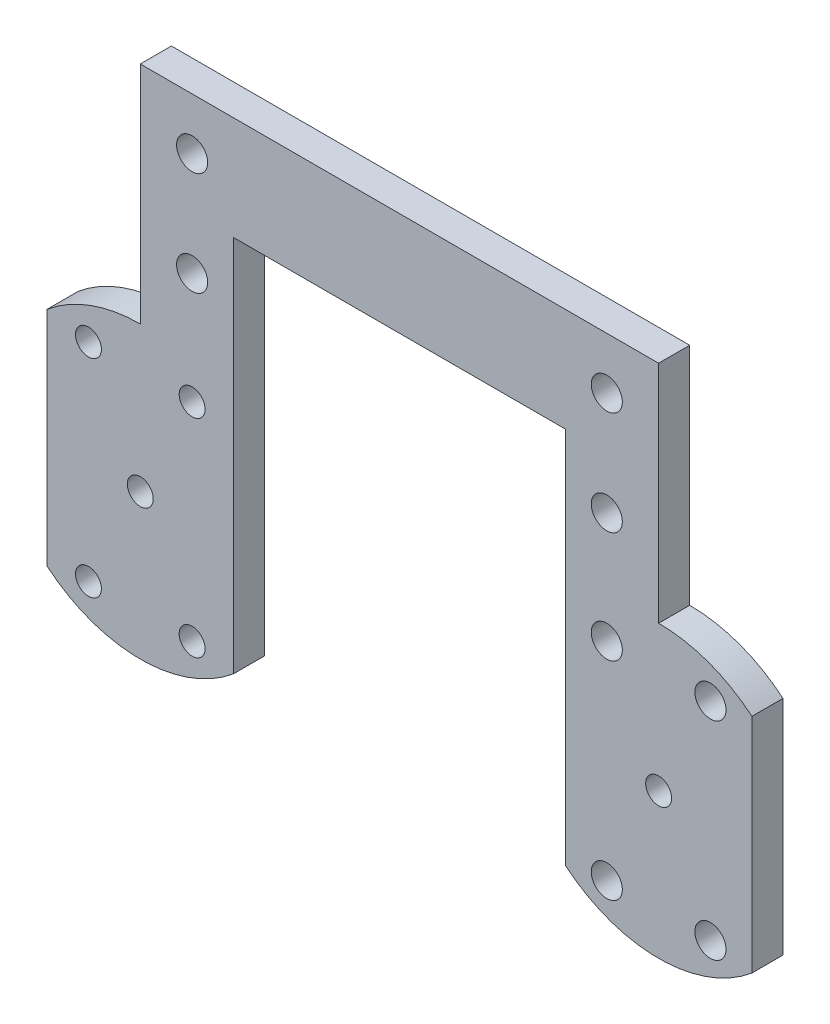
SolidWorks part; units mm, degrees
ref_plane "Front Plane" through (0, 0, 0) normal (0, 0, 1) x (1, 0, 0)
ref_plane "Top Plane" through (0, 0, 0) normal (0, 1, 0) x (1, 0, 0)
ref_plane "Right Plane" through (0, 0, 0) normal (1, 0, 0) x (0, 0, -1)
sketch "Sketch1" plane through (0, 0, 0) normal (0, 0, 1) x (1, 0, 0)
  line L0 (-9, 10.7238) -> (-9, -10.7238)
  line L1 (9, -10.7238) -> (41, -10.7238)
  line L2 (-9, 0) -> (9, 0) construction
  line L3 (-5, 10) -> (5, -10) construction
  line L4 (-5, -10) -> (5, 10) construction
  line L5 (9, 10.7238) -> (41, 10.7238)
  line L6 (0, 0) -> (50, 0) construction
  line L7 (59, 10.7238) -> (59, -10.7238)
  line L8 (45, 10) -> (55, -10) construction
  line L9 (55, 10) -> (45, -10) construction
  arc A0 (9, 10.7238) -> (-9, 10.7238) centre (0, 0) ccw
  arc A1 (-9, -10.7238) -> (9, -10.7238) centre (0, 0) ccw
  circle A2 centre (0, 0) radius 1.25
  circle A3 centre (-5, 10) radius 1.25
  circle A4 centre (5, 10) radius 1.25
  circle A5 centre (-5, -10) radius 1.25
  circle A6 centre (5, -10) radius 1.25
  arc A7 (41, -10.7238) -> (59, -10.7238) centre (50, 0) ccw
  arc A8 (59, 10.7238) -> (41, 10.7238) centre (50, 0) ccw
  circle A9 centre (50, 0) radius 1.25
  circle A10 centre (45, 10) radius 1.5
  circle A11 centre (55, 10) radius 1.5
  circle A12 centre (45, -10) radius 1.5
  circle A13 centre (55, -10) radius 1.5
  circle A14 centre (25, 0) radius 1.25
  circle A15 centre (25, 5) radius 1.25
  circle A16 centre (25, -5) radius 1.25
  circle A17 centre (35, 0) radius 1.25
  circle A18 centre (15, 0) radius 1.25
  circle A19 centre (35, 5) radius 1.25
  circle A20 centre (35, -5) radius 1.25
  circle A21 centre (15, -5) radius 1.25
  circle A22 centre (15, 5) radius 1.25
  point P7 (0, 0)
  point P18 (0, 0)
  point P25 (50, 0)
  point P36 (50, 0)
  dimension "D2" = 14
  dimension "D3" = 2.5
  dimension "D6" = 2.5
  dimension "D8" = 3
  dimension "D11" = 2.5
  dimension "D1" = 18
  dimension "D4" = 20
  dimension "D5" = 10
  dimension "D7" = 50
  dimension "D9" = 10
  dimension "D10" = 20
  dimension "D12" = 5
  dimension "D13" = 10
  dimension "D14" = 10
  dimension "D15" = 5
extrude "Boss-Extrude1" add sketch "Sketch1" along normal blind 3
sketch "Sketch2" plane through (0, 0, 3) normal (0, 0, 1) x (1, 0, 0)
  line L0 (0, 14) -> (0, 35.7238)
  line L1 (0, 35.7238) -> (50, 35.7238)
  line L2 (50, 35.7238) -> (50, 14)
  line L3 (9, 10.7238) -> (9, 25.7238)
  line L4 (9, 25.7238) -> (41, 25.7238)
  line L5 (41, 25.7238) -> (41, 10.7238)
  line L6 (41, 10.7238) -> (9, 10.7238) construction
  arc A0 (59, 10.7238) -> (41, 10.7238) centre (50, 0) ccw construction
  arc A1 (9, 10.7238) -> (-9, 10.7238) centre (0, 0) ccw construction
  arc A2 (9, 10.7238) -> (0, 14) centre (0, 0) ccw
  arc A3 (41, 10.7238) -> (50, 14) centre (50, 0) cw
  circle A4 centre (5, 30.7238) radius 1.5
  circle A5 centre (45, 30.7238) radius 1.5
  circle A6 centre (45, 20.7238) radius 1.5
  circle A7 centre (5, 20.7238) radius 1.5
  point P30 (0, 0)
  point P31 (0, 0)
  point P32 (0, 0)
  dimension "D3" = 3
  dimension "D1" = 15
  dimension "D2" = 10
  dimension "D4" = 5
  dimension "D5" = 5
  dimension "D6" = 40
  dimension "D7" = 10
  dimension "D8" = 10
extrude "Boss-Extrude2" add sketch "Sketch2" against normal up to surface (3 mm away) up to face at (25, 0, 0)
sketch "Sketch3" plane through (0, 0, 3) normal (0, 0, 1) x (1, 0, 0)
  line L1 (9, 10.7238) -> (41, 10.7238)
  line L2 (9, 10.7238) -> (9, -10.7238)
  line L3 (9, -10.7238) -> (41, -10.7238)
  line L4 (41, 10.7238) -> (41, -10.7238)
extrude "Cut-Extrude1" cut sketch "Sketch3" against normal through all
